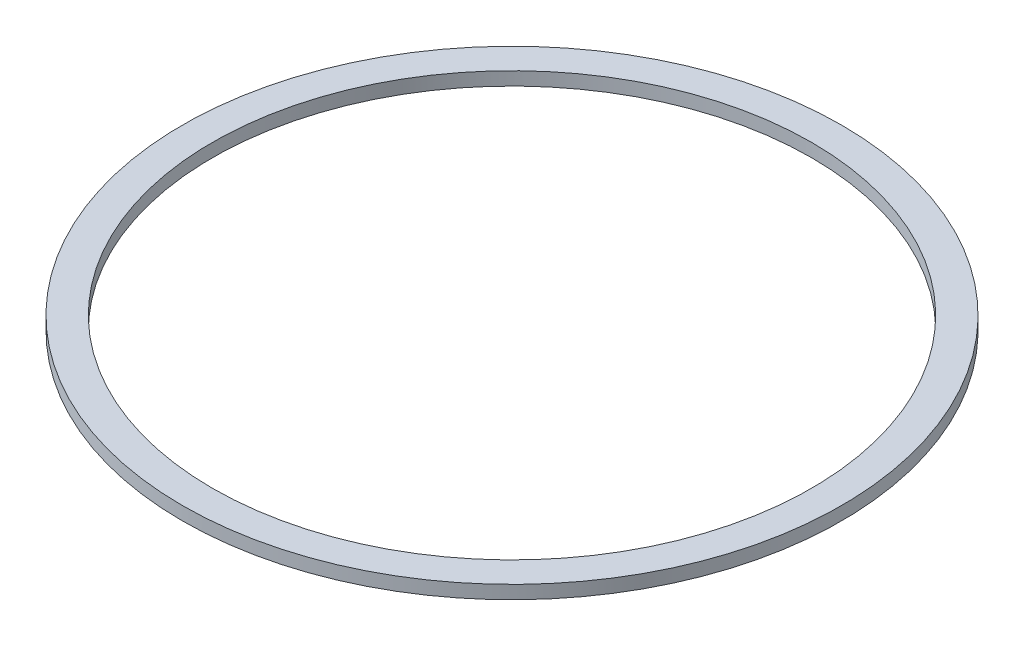
SolidWorks part; units mm, degrees
ref_plane "Plano frontal" through (0, 0, 0) normal (0, 0, 1) x (1, 0, 0)
ref_plane "Plano superior" through (0, 0, 0) normal (0, 1, 0) x (1, 0, 0)
ref_plane "Plano direito" through (0, 0, 0) normal (1, 0, 0) x (0, 0, -1)
sketch "Esboço1" plane through (0, 0, 0) normal (0, 1, 0) x (1, 0, 0)
  circle A0 centre (0, 0) radius 99
  circle A1 centre (0, 0) radius 90
  dimension "D1" = 198
  dimension "D2" = 180
extrude "Ressalto-extrusão1" add sketch "Esboço1" along normal blind 4
